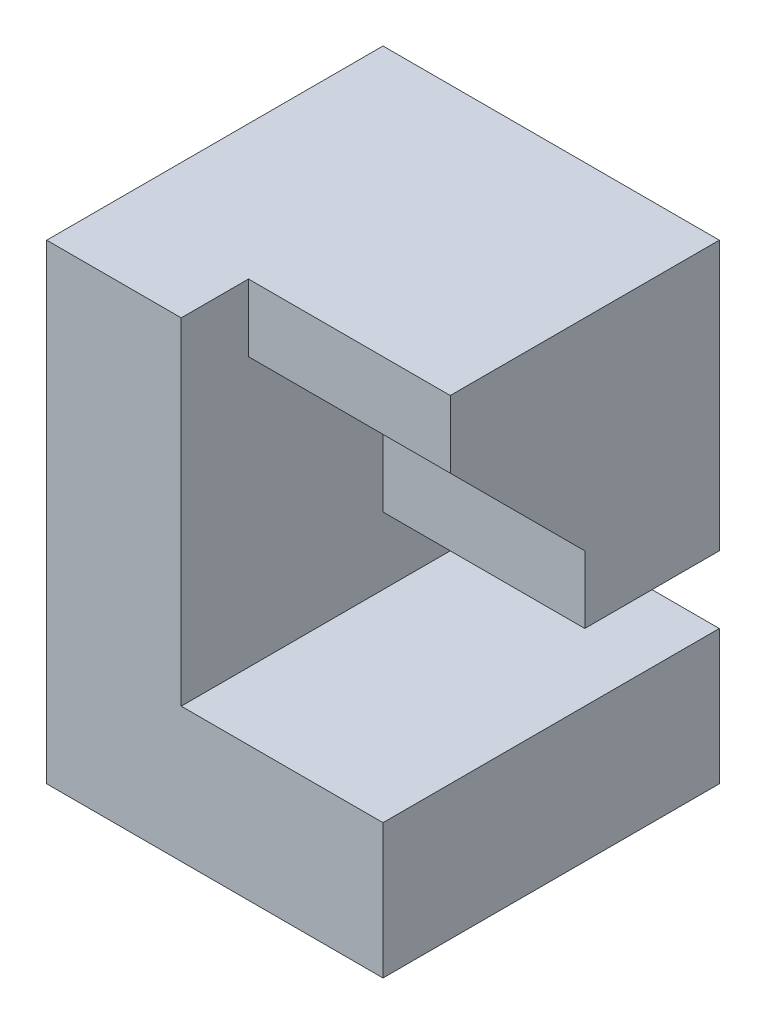
SolidWorks part; units mm, degrees
ref_plane "Front" through (0, 0, 0) normal (0, 0, 1) x (1, 0, 0)
ref_plane "Top" through (0, 0, 0) normal (0, 1, 0) x (1, 0, 0)
ref_plane "Right" through (0, 0, 0) normal (1, 0, 0) x (0, 0, -1)
sketch "Sketch1" plane through (0, 0, 0) normal (1, 0, 0) x (0, 0, -1)
  line L1 (2.5, -3.5) -> (-2.5, -3.5)
  line L2 (2.5, -3.5) -> (2.5, 3.5)
  line L3 (2.5, 3.5) -> (-2.5, 3.5)
  line L4 (-2.5, -3.5) -> (-2.5, 3.5)
  line L5 (2.5, -3.5) -> (-2.5, 3.5) construction
  line L6 (2.5, 3.5) -> (-2.5, -3.5) construction
  point P0 (0, 0)
  dimension "D1" = 5
  dimension "D2" = 7
extrude "Boss-Extrude1" add sketch "Sketch1" along normal blind 5
sketch "Sketch2" plane through (5, 0, 0) normal (1, 0, 0) x (0, 0, -1)
  line L0 (2.5, -1.5) -> (-2.5, -1.5)
  line L1 (2.5, -3.5) -> (2.5, 3.5) construction
  line L2 (-2.5, 3.5) -> (-2.5, -3.5) construction
  line L3 (-2.5, -1.5) -> (-2.5, 3.5)
  line L4 (-2.5, 3.5) -> (-1.5, 3.5)
  line L5 (2.5, 3.5) -> (-2.5, 3.5) construction
  line L6 (-1.5, 3.5) -> (-1.5, 2.5)
  line L7 (-1.5, 2.5) -> (0.5, 0.5)
  line L8 (0.5, 0.5) -> (0.5, -0.5)
  line L9 (0.5, -0.5) -> (2.5, -0.5)
  line L10 (2.5, -0.5) -> (2.5, -1.5)
  dimension "D1" = 1
  dimension "D2" = 1
  dimension "D3" = 2
  dimension "D4" = 2
  dimension "D5" = 1
  dimension "D6" = 5
extrude "Cut-Extrude1" cut sketch "Sketch2" against normal blind 3
